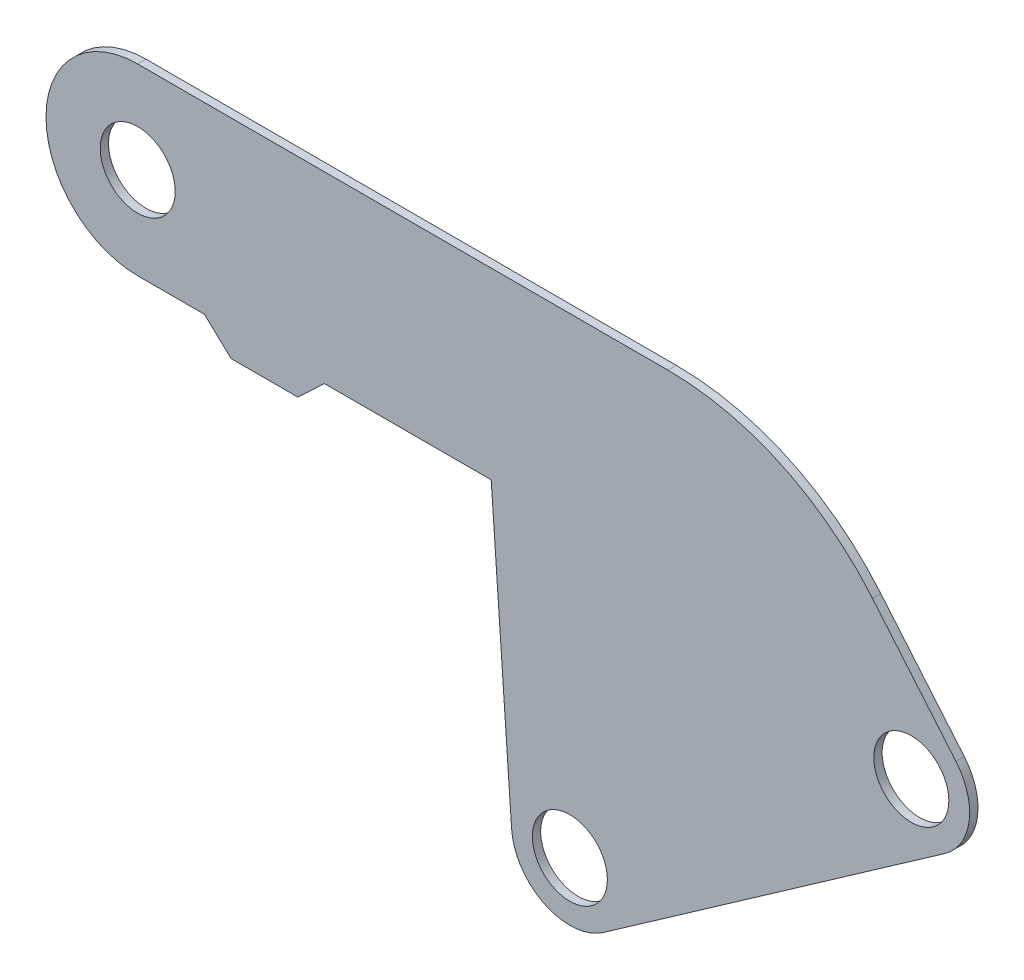
SolidWorks part; units mm, degrees
material "ABS PC"
ref_plane "Front Plane" through (0, 0, 0) normal (0, 0, 1) x (1, 0, 0)
ref_plane "Top Plane" through (0, 0, 0) normal (0, 1, 0) x (1, 0, 0)
ref_plane "Right Plane" through (0, 0, 0) normal (1, 0, 0) x (0, 0, -1)
sketch "Sketch1" plane through (0, 0, 0) normal (0, 0, 1) x (1, 0, 0)
  line L0 (0, 0) -> (0, 215.9) construction
  line L1 (133.35, 0) -> (133.35, 171.45) construction
  line L2 (0.0421, 0) -> (133.3921, 0) construction
  line L3 (50.8, 0) -> (50.8, 123.825) construction
  line L4 (508, 0) -> (508, 50000) construction
  line L11 (133.35, 171.45) -> (0, 171.45) construction
  line L20 (508, 457.2) -> (482.6, 457.2) construction
  line L22 (-203.2, 0) -> (-203.2, 53.1862) construction
  line L31 (-203.2, 520.7) -> (50.8, 520.7) construction
  line L48 (294.6125, 162.3041) -> (164.5721, 71.2488) construction
  line L52 (0, 180.975) -> (134.62, 180.975) construction
  line L53 (134.62, 180.975) -> (142.4012, 69.6985)
  line L62 (177.3198, 53.0432) -> (307.3602, 144.0984)
  line L66 (25.4, 180.975) -> (35.56, 171.45)
  line L67 (35.56, 171.45) -> (60.96, 171.45)
  line L68 (60.96, 171.45) -> (71.12, 180.975)
  line L69 (71.12, 180.975) -> (134.62, 180.975)
  line L70 (0, 250.825) -> (201.9704, 250.825)
  line L71 (279.8005, 214.5322) -> (311.6378, 176.59)
  line L72 (0, 180.975) -> (25.4, 180.975)
  circle A11 centre (508, 75.057) radius 75.057 construction
  arc A19 (0, 250.825) -> (0, 180.975) centre (0, 215.9) ccw
  circle A23 centre (294.6125, 162.3041) radius 14.2875
  circle A24 centre (164.5721, 71.2488) radius 14.2875
  circle A25 centre (0, 215.9) radius 14.2875
  arc A28 (201.9704, 250.825) -> (279.8005, 214.5322) centre (201.9704, 149.225) cw
  circle A29 centre (294.6125, 162.3041) radius 12.7 construction
  arc A32 (311.6378, 176.59) -> (307.3602, 144.0984) centre (294.6125, 162.3041) cw
  circle A33 centre (164.5721, 71.2488) radius 12.7 construction
  arc A34 (142.4012, 69.6985) -> (177.3198, 53.0432) centre (164.5721, 71.2488) ccw
  point P17 (-177.8, 889)
  point P27 (177.3198, 53.0432)
  point P38 (201.9704, 250.825)
  point P42 (134.62, 180.975)
  dimension "D4" = 304.8
  dimension "D9" = 49.53
  dimension "D10" = 134.62
  dimension "D11" = 158.75
  dimension "D12" = 59
  dimension "D13" = 150.114
  dimension "D14" = 94
  dimension "D21" = 25.4
  dimension "D3" = 171.45
  dimension "D6" = 130
  dimension "D15" = 25.4
  dimension "D23" = 25.4
  dimension "D8" = 69.85
  dimension "D28" = 28.575
  dimension "D29" = 9.525
  dimension "D30" = 101.6
  dimension "D24" = 22.225
  dimension "D26" = 25.4
  dimension "D1" = 82.55
  dimension "D2" = 215.9
  dimension "D5" = 50.8
  dimension "D7" = 457.2
  dimension "D17" = 457.2
  dimension "D18" = 177.8
  dimension "D19" = 889
  dimension "D20" = 25.4
  dimension "4.5" = 203.2
  dimension "D27" = 63.5
extrude "Boss-Extrude1" add sketch "Sketch1" along normal blind 3.175
